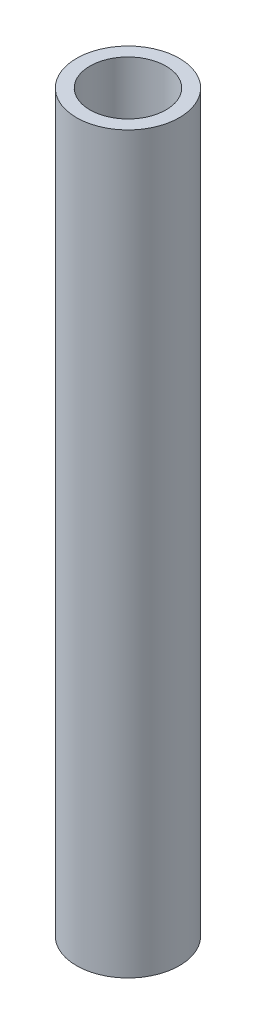
SolidWorks part; units mm, degrees
ref_plane "Front" through (0, 0, 0) normal (0, 0, 1) x (1, 0, 0)
ref_plane "Top" through (0, 0, 0) normal (0, 1, 0) x (1, 0, 0)
ref_plane "Right" through (0, 0, 0) normal (1, 0, 0) x (0, 0, -1)
sketch "Sketch1" plane through (0, 0, 0) normal (0, 1, 0) x (1, 0, 0)
  circle A0 centre (0, 0) radius 19.05
  dimension "D1" = 38.1
extrude "Boss-Extrude1" add sketch "Sketch1" along normal blind 272.1102
sketch "Sketch2" plane through (0, 272.1102, 0) normal (0, 1, 0) x (1, 0, 0)
  circle A0 centre (0, 0) radius 12.7
  dimension "D1" = 25.4
extrude "Cut-Extrude1" cut sketch "Sketch2" against normal through all
hole_wizard "1-1/4-7 Tapped Hole1" positions "Sketch6" profile "Sketch5" tap size "1-1/4-7" standard "ANSI Inch"
sketch "Sketch6" plane through (0, 272.1102, 0) normal (0, 1, 0) x (1, 0, 0)
  point P0 (0, 0)
sketch "Sketch5" plane through (0, 272.1102, 0) normal (1, 0, 0) x (0, 0, 1)
  line L0 (0, 0) -> (0, 57.4878)
  line L1 (0, 57.4878) -> (14.0894, 49.022)
  line L2 (14.0894, 49.022) -> (14.0894, 0)
  line L5 (14.0894, 0) -> (0, 0)
  line L10 (0, 57.4878) -> (-14.0894, 49.022) construction
  line L11 (0, -6.35) -> (0, 107.95) construction
  dimension "Tap Drill Dia." = 28.1788
  dimension "Tap Drill Depth" = 49.022
  dimension "Drill Angle" = 118
cosmetic thread "Hole Thread1" parameters "D1"=38.1, "D2"=31.75
hole_wizard "1-1/4-7 Tapped Hole2" positions "Sketch8" profile "Sketch7" tap size "1-1/4-7" standard "ANSI Inch"
sketch "Sketch8" plane through (0, 0, 0) normal (0, -1, 0) x (-1, 0, 0)
  point P0 (0, 0)
sketch "Sketch7" plane through (0, 0, 0) normal (1, 0, 0) x (0, 0, -1)
  line L0 (0, 0) -> (0, 57.4878)
  line L1 (0, 57.4878) -> (14.0894, 49.022)
  line L2 (14.0894, 49.022) -> (14.0894, 0)
  line L5 (14.0894, 0) -> (0, 0)
  line L10 (0, 57.4878) -> (-14.0894, 49.022) construction
  line L11 (0, -6.35) -> (0, 107.95) construction
  dimension "Tap Drill Dia." = 28.1788
  dimension "Tap Drill Depth" = 49.022
  dimension "Drill Angle" = 118
cosmetic thread "Hole Thread2" parameters "D1"=38.1, "D2"=31.75
